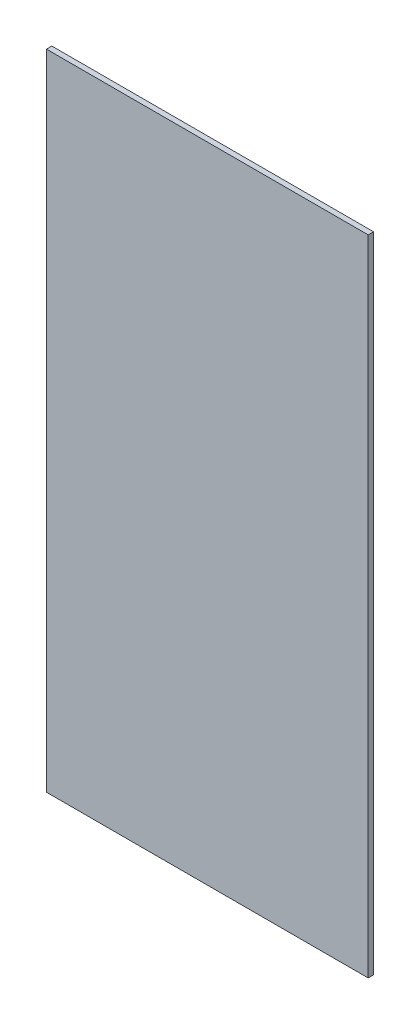
SolidWorks part; units mm, degrees
ref_plane "Front Plane" through (0, 0, 0) normal (0, 0, 1) x (1, 0, 0)
ref_plane "Top Plane" through (0, 0, 0) normal (0, 1, 0) x (1, 0, 0)
ref_plane "Right Plane" through (0, 0, 0) normal (1, 0, 0) x (0, 0, -1)
sketch "Sketch1" plane through (0, 0, 0) normal (0, 0, 1) x (1, 0, 0)
  line L0 (0, 152.4) -> (0, -152.4) construction
  line L1 (-76.2, 152.4) -> (76.2, 152.4)
  line L2 (-76.2, 152.4) -> (-76.2, -152.4)
  line L3 (-76.2, -152.4) -> (76.2, -152.4)
  line L4 (76.2, 152.4) -> (76.2, -152.4)
  dimension "D1" = 304.8
  dimension "D2" = 152.4
extrude "Boss-Extrude1" add sketch "Sketch1" along normal mid plane 2.54
